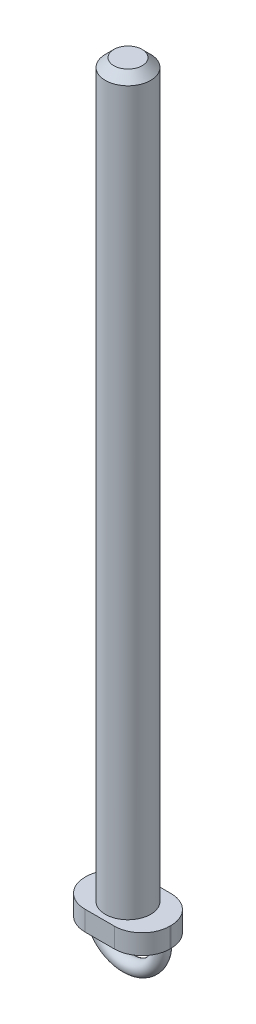
SolidWorks part; units mm, degrees
ref_plane "Plano frontal" through (0, 0, 0) normal (0, 0, 1) x (1, 0, 0)
ref_plane "Plano superior" through (0, 0, 0) normal (0, 1, 0) x (1, 0, 0)
ref_plane "Plano direito" through (0, 0, 0) normal (1, 0, 0) x (0, 0, -1)
sketch "Esboço1" plane through (0, 0, 0) normal (0, 0, 1) x (1, 0, 0)
  line L0 (0, 0) -> (11, 0)
  line L1 (11, 0) -> (11, 3.5)
  line L2 (11, 3.5) -> (4, 3.5)
  line L3 (4, 3.5) -> (4, 132.66)
  line L4 (4, 132.66) -> (0, 132.66)
  line L5 (0, 132.66) -> (0, 0) construction
  line L6 (0, 0) -> (0, 132.66)
  dimension "D1" = 8
  dimension "D2" = 22
  dimension "D3" = 3.5
  dimension "D4" = 129.16
revolve "Revolução1" add sketch "Esboço1" angle 360 about L5
sketch "Esboço2" plane through (0, 0, 0) normal (0, -1, 0) x (1, 0, 0)
  line L1 (2.6, -5) -> (-2.6, -5)
  line L2 (7.5, -0.1) -> (7.5, 0.1)
  line L3 (2.6, 5) -> (-2.6, 5)
  line L4 (-7.5, -0.1) -> (-7.5, 0.1)
  line L5 (7.5, -5) -> (-7.5, 5) construction
  line L6 (7.5, 5) -> (-7.5, -5) construction
  arc A1 (-2.6, -5) -> (-7.5, -0.1) centre (-2.6, -0.1) cw
  arc A2 (-2.6, 5) -> (-7.5, 0.1) centre (-2.6, 0.1) ccw
  arc A3 (7.5, 0.1) -> (2.6, 5) centre (2.6, 0.1) ccw
  arc A4 (2.6, -5) -> (7.5, -0.1) centre (2.6, -0.1) ccw
  point P0 (0, 0)
  circle M3 centre (0, 0) radius 11
  dimension "D3" = 4.9
  dimension "D1" = 10
  dimension "D2" = 15
extrude "Corte-extrusão1" cut sketch "Esboço2" against normal blind 10 contours L4 M3 | L3 M3 | L2 M3 | L1 M3
sketch "Esboço7" plane through (0, 0, 0) normal (0, -1, 0) x (-1, 0, 0)
  circle A0 centre (6, 0) radius 1.25
  dimension "D1" = 2.5
  dimension "D2" = 6
sketch "Esboço9" plane through (0, 0, 0) normal (0, 0, 1) x (1, 0, 0)
  arc A0 (-6, 0) -> (6, 0) centre (0, 0) ccw
  dimension "D1" = 12
sweep "Varredura1" add profiles "Esboço7" path "Esboço9"
chamfer "Chanfro1" distance 1.5 angle 45 1 edges at (-4, 132.66, 0)
